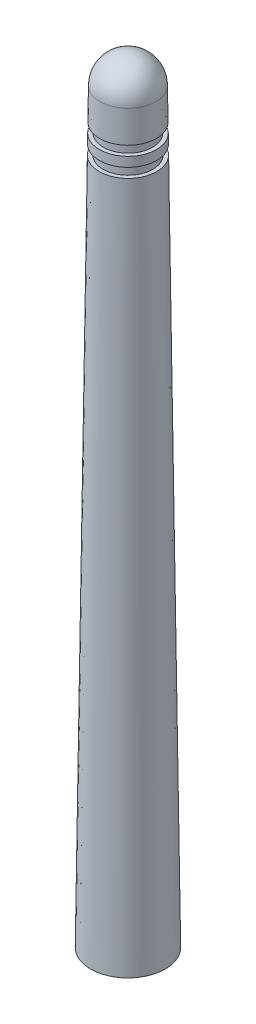
SolidWorks part; units mm, degrees
ref_plane "Alzado" through (0, 0, 0) normal (0, 0, 1) x (1, 0, 0)
ref_plane "Planta" through (0, 0, 0) normal (0, 1, 0) x (1, 0, 0)
ref_plane "Vista lateral" through (0, 0, 0) normal (1, 0, 0) x (0, 0, -1)
sketch "Croquis1" plane through (0, 0, 0) normal (0, 0, 1) x (1, 0, 0)
  line L0 (0, 0) -> (-5, 0)
  line L1 (-5, 0) -> (-3.8508, 91.9383)
  line L2 (0, 103.75) -> (0, 100)
  line L3 (0, 100) -> (0, 0)
  line L4 (-3.8031, 95.75) -> (-3.3031, 95.75)
  line L5 (-3.3031, 95.75) -> (-3.3031, 94.4794)
  line L6 (-3.3031, 94.4794) -> (-3.819, 94.4794)
  line L7 (-3.8349, 93.2089) -> (-3.3349, 93.2089)
  line L8 (-3.3349, 93.2089) -> (-3.3349, 91.9383)
  line L9 (-3.3349, 91.9383) -> (-3.8508, 91.9383)
  line L10 (-3.8031, 95.75) -> (-3.75, 100)
  line L11 (-3.8349, 93.2089) -> (-3.819, 94.4794)
  arc A0 (-3.75, 100) -> (0, 103.75) centre (0, 100) cw
  dimension "D3" = 100
  dimension "D1" = 5
  dimension "D2" = 3.75
  dimension "D4" = 0.5
  dimension "D5" = 8
revolve "Revolución1" add sketch "Croquis1" angle 360 about L3
